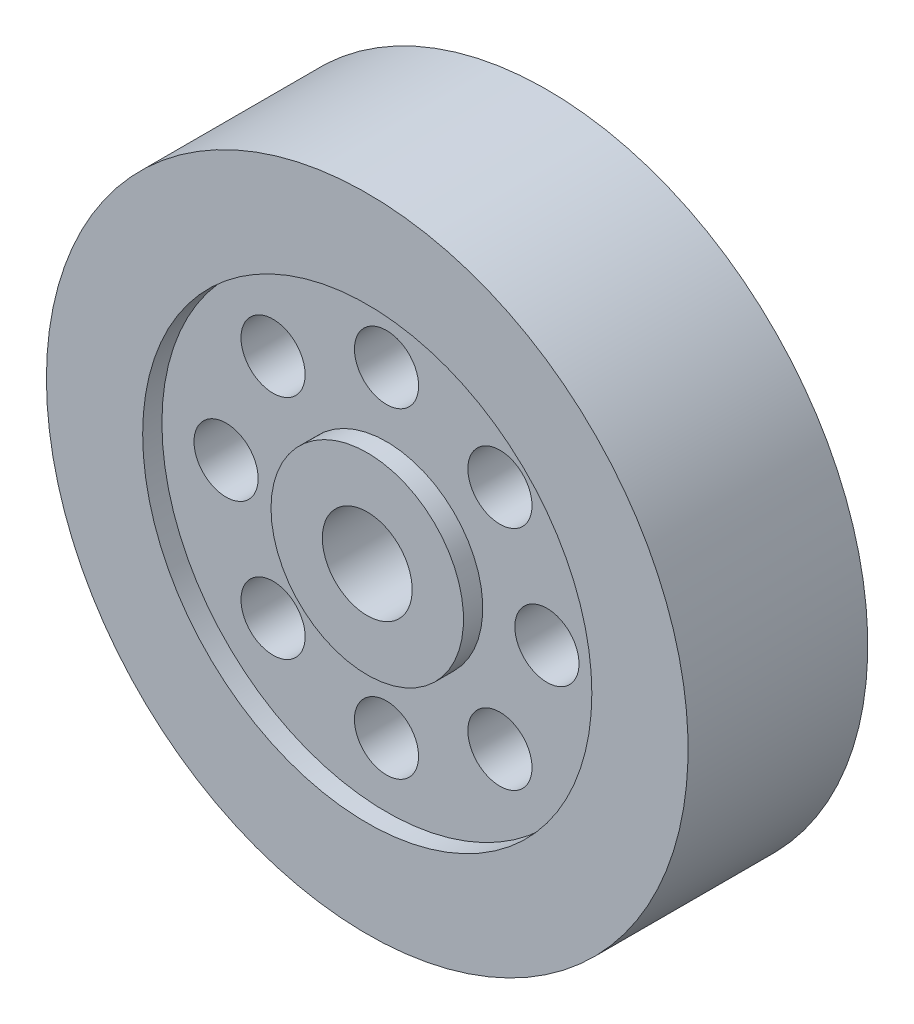
SolidWorks part; units mm, degrees
material "Natural Rubber"
ref_plane "Front" through (0, 0, 0) normal (0, 0, 1) x (1, 0, 0)
ref_plane "Top" through (0, 0, 0) normal (0, 1, 0) x (1, 0, 0)
ref_plane "Right" through (0, 0, 0) normal (1, 0, 0) x (0, 0, -1)
sketch "Sketch1" plane through (0, 0, 0) normal (0, 1, 0) x (1, 0, 0)
  line L0 (0, 184.0452) -> (0, -207.9643) construction
  line L1 (-269.9753, 0) -> (289.5867, 0) construction
  line L2 (7, 0) -> (7, 14)
  line L3 (7, 14) -> (15, 14)
  line L4 (15, 14) -> (15, 11)
  line L5 (15, 11) -> (35, 11)
  line L6 (35, 11) -> (35, 14)
  line L7 (35, 14) -> (50, 14)
  line L8 (50, 14) -> (50, 0)
  line L9 (50, 0) -> (7, 0)
  dimension "D1" = 100
  dimension "D2" = 70
  dimension "D3" = 30
  dimension "D4" = 14
  dimension "D5" = 28
  dimension "D6" = 3
revolve "Revolve1" add sketch "Sketch1" angle 360 about L0
sketch "Sketch2" plane through (0, 0, -11) normal (0, 0, -1) x (-1, 0, 0)
  circle A0 centre (0, 0) radius 25 construction
  circle A1 centre (0, -25) radius 5
  dimension "D1" = 50
  dimension "D2" = 10
extrude "Cut-Extrude1" cut sketch "Sketch2" against normal through all
pattern_circular "CirPattern1" count 8 over 360 about axis through (0, 0, 0) along (0, 0, 1) of "Cut-Extrude1"
mirror "Mirror1" about plane through (0, 0, 0) normal (0, 0, 1) of bodies 103
